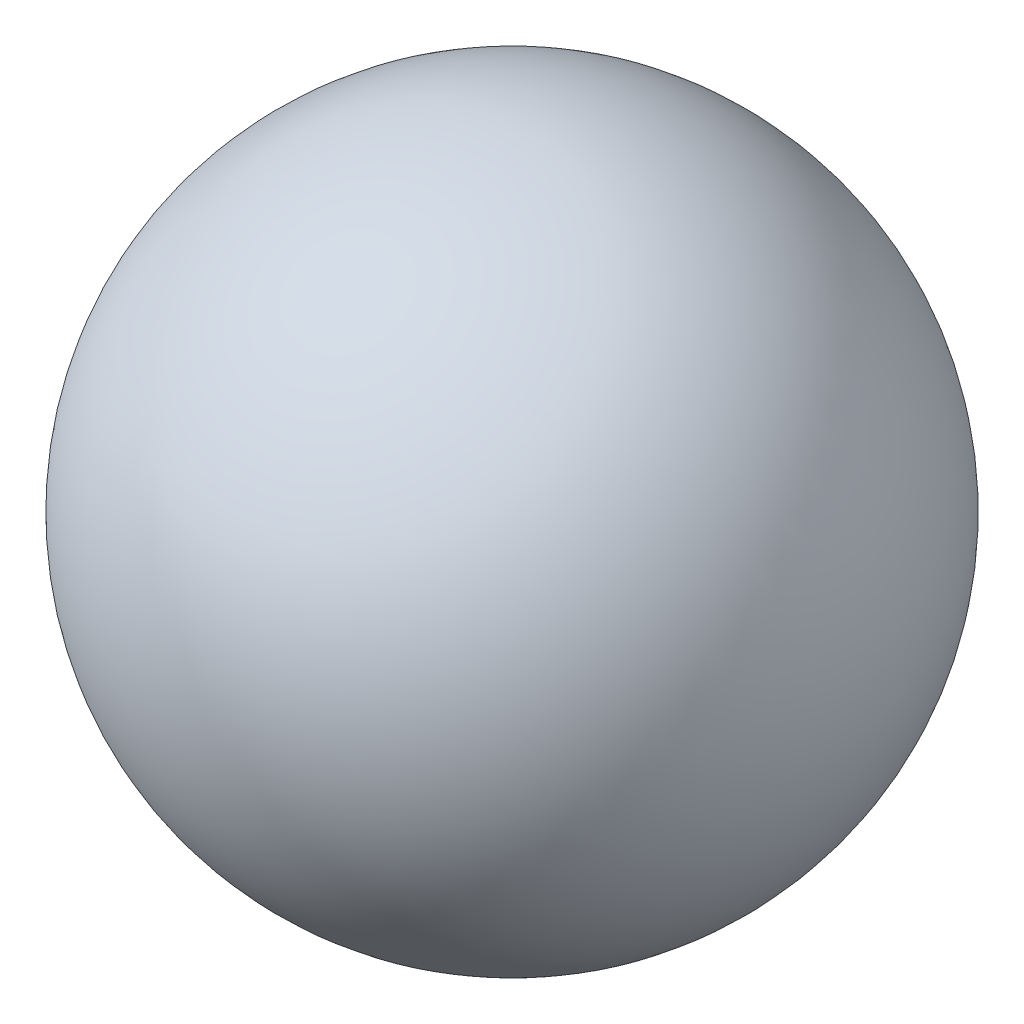
SolidWorks part; units mm, degrees
material "Plain Carbon Steel"
ref_plane "Front Plane" through (0, 0, 0) normal (0, 0, 1) x (1, 0, 0)
ref_plane "Top Plane" through (0, 0, 0) normal (0, 1, 0) x (1, 0, 0)
ref_plane "Right Plane" through (0, 0, 0) normal (1, 0, 0) x (0, 0, -1)
sketch "Sketch1" plane through (0, 0, 0) normal (0, 0, 1) x (1, 0, 0)
  line L0 (0, 2.6938) -> (0, -2.9778) construction
  line L1 (0, 1.25) -> (0, -1.25)
  arc A0 (0, -1.25) -> (0, 1.25) centre (0, 0) ccw
  dimension "D1" = 2.5
revolve "Revolve3" add sketch "Sketch1" angle 360 about L0
